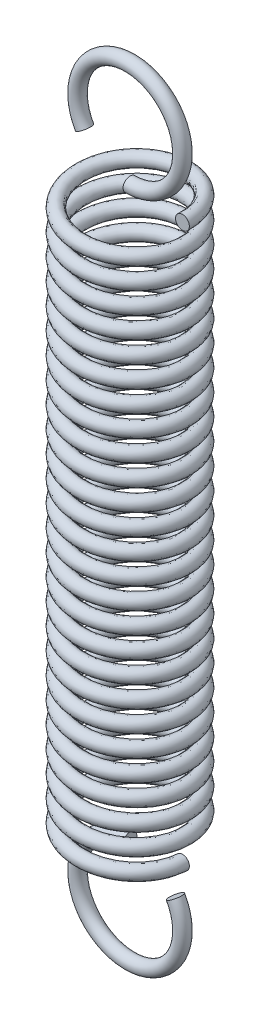
SolidWorks part; units mm, degrees
material "AISI 304"
ref_plane "Front Plane" through (0, 0, 0) normal (0, 0, 1) x (1, 0, 0)
ref_plane "Top Plane" through (0, 0, 0) normal (0, 1, 0) x (1, 0, 0)
ref_plane "Right Plane" through (0, 0, 0) normal (1, 0, 0) x (0, 0, -1)
sketch "Sketch1" plane through (0, 0, 0) normal (0, 0, 1) x (1, 0, 0)
  line L0 (0, 0) -> (14.826, 0) construction
  line L1 (0, 0) -> (0, -3) construction
  line L2 (-3, 0) -> (-3, -3) construction
  line L3 (-3, 0) -> (3, 0)
  line L4 (-3, 0) -> (-3, 28)
  line L5 (-3, 28) -> (3, 28)
  line L6 (3, 0) -> (3, 28)
  line L7 (3, 0) -> (3, -3) construction
  line L8 (0, 31) -> (0, 0) construction
  line L10 (0, 34) -> (-3, 34) construction
  line L11 (0, -6) -> (-3, -6) construction
  line L12 (0, 29) -> (-3.8337, 29) construction
  line L13 (-3, 23) -> (3, 23) construction
  circle A0 centre (0, -3) radius 3
  circle A1 centre (0, 31) radius 3
  circle A2 centre (0, 26) radius 3 construction
  circle A3 centre (2.65, 0) radius 0.35
  circle A4 centre (0, 31) radius 2.3
  circle A5 centre (0, -3) radius 2.3
  circle A6 centre (0, -0.35) radius 0.35
  dimension "D1" = 6
  dimension "D4" = 0.7
  dimension "D2" = 40
  dimension "D3" = 35
sketch "Sketch2" plane through (0, 0, 0) normal (0, 1, 0) x (1, 0, 0)
  circle A0 centre (0, 0) radius 2.65
curve "Helix/Spiral1" pitch 1.0769 height 28 turns 26
sketch "Sketch3" plane through (0, 0, 0) normal (0, 0, 1) x (1, 0, 0)
  circle A0 centre (2.65, 0) radius 0.35 construction
  circle A1 centre (2.65, 0) radius 0.35
sweep "Sweep1" add profiles "Sketch3" path "Helix/Spiral1"
sketch "Sketch4" plane through (0, 0, 0) normal (1, 0, 0) x (0, 0, -1)
  line L0 (0, 31) -> (0, 0) construction
  line L1 (0, -0.35) -> (0, 29) construction
  line L2 (0, -3) -> (-3.9017, -3) construction
  line L3 (0, 31) -> (-2.4397, 31) construction
  line L6 (0, 28.7) -> (-0.8196, 28.7) construction
  circle A0 centre (0, 28.35) radius 0.35 construction
  circle A1 centre (0, -0.35) radius 0.35
revolve "Revolve1" add sketch "Sketch4" angle 300 about L2
sketch "Sketch7" plane through (0, 0, 0) normal (1, 0, 0) x (0, 0, -1)
  line L0 (0, 31) -> (-2.4397, 31) construction
  line L1 (0, 31) -> (-2.4397, 31) construction
  circle A0 centre (0, 28.35) radius 0.35 construction
  circle A1 centre (0, 28.35) radius 0.35
revolve "Revolve2" add sketch "Sketch7" angle 300 about L1
